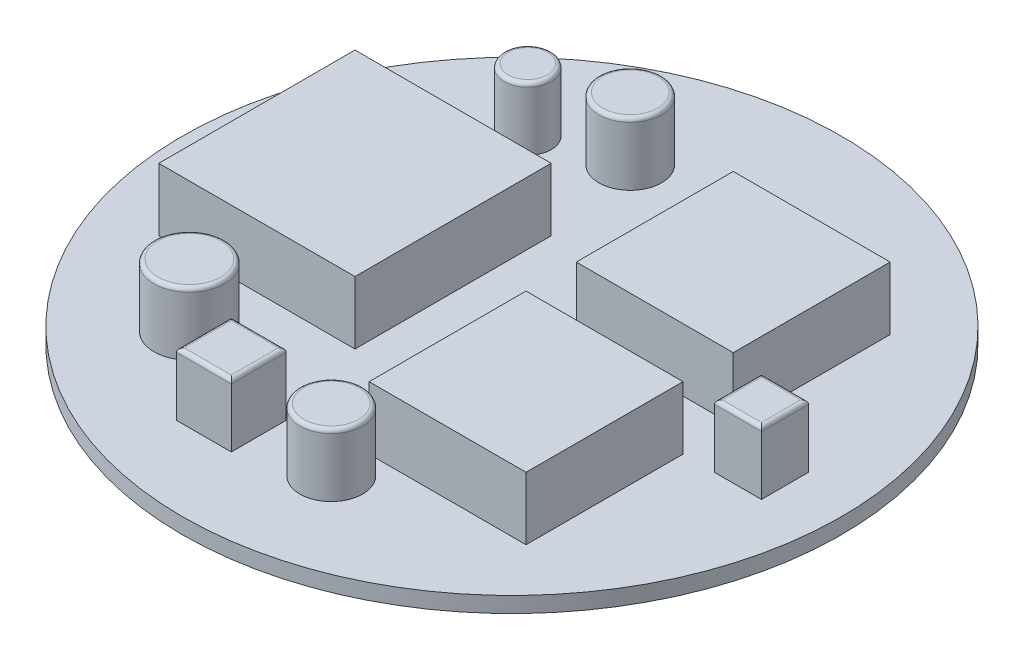
SolidWorks part; units mm, degrees
ref_plane "Front Plane" through (0, 0, 0) normal (0, 0, 1) x (1, 0, 0)
ref_plane "Top Plane" through (0, 0, 0) normal (0, 1, 0) x (1, 0, 0)
ref_plane "Right Plane" through (0, 0, 0) normal (1, 0, 0) x (0, 0, -1)
sketch "Sketch1" plane through (0, 0, 0) normal (0, 1, 0) x (1, 0, 0)
  circle A0 centre (0, 0) radius 42
extrude "Boss-Extrude1" add sketch "Sketch1" along normal blind 2
sketch "Sketch2" plane through (0, 2, 0) normal (0, 1, 0) x (1, 0, 0)
  line L0 (0, 0) -> (8.0339, 0) construction
  line L1 (-32.5, -12.5) -> (-7.5, -12.5)
  line L2 (-32.5, -12.5) -> (-32.5, 12.5)
  line L3 (-32.5, 12.5) -> (-7.5, 12.5)
  line L4 (-7.5, -12.5) -> (-7.5, 12.5)
  line L5 (-32.5, -12.5) -> (-7.5, 12.5) construction
  line L6 (-32.5, 12.5) -> (-7.5, -12.5) construction
  line L7 (5, 23.2036) -> (25, 23.2036)
  line L8 (5, 23.2036) -> (5, 3.2036)
  line L9 (5, 3.2036) -> (25, 3.2036)
  line L10 (25, 23.2036) -> (25, 3.2036)
  line L11 (5, 23.2036) -> (25, 3.2036) construction
  line L12 (5, 3.2036) -> (25, 23.2036) construction
  line L13 (25, -23.2036) -> (25, -3.2036)
  line L14 (5, -3.2036) -> (25, -3.2036)
  line L15 (5, -23.2036) -> (5, -3.2036)
  line L16 (5, -23.2036) -> (25, -23.2036)
  line L18 (-4.0182, -24.7434) -> (-11.0182, -24.7434)
  line L19 (-4.0182, -24.7434) -> (-4.0182, -31.7434)
  line L20 (-4.0182, -31.7434) -> (-11.0182, -31.7434)
  line L21 (-11.0182, -24.7434) -> (-11.0182, -31.7434)
  line L22 (-4.0182, -24.7434) -> (-11.0182, -31.7434) construction
  line L23 (-4.0182, -31.7434) -> (-11.0182, -24.7434) construction
  line L24 (29.0021, 2.7964) -> (35.0021, 2.7964)
  line L25 (29.0021, 2.7964) -> (29.0021, -3.2036)
  line L26 (29.0021, -3.2036) -> (35.0021, -3.2036)
  line L27 (35.0021, 2.7964) -> (35.0021, -3.2036)
  line L28 (29.0021, 2.7964) -> (35.0021, -3.2036) construction
  line L29 (29.0021, -3.2036) -> (35.0021, 2.7964) construction
  circle A2 centre (-20, 22.0202) radius 3
  circle A3 centre (-10.3025, 25.3777) radius 4
  circle A4 centre (-20, -21.1145) radius 4.5
  circle A5 centre (5, -28.0205) radius 4
  point P0 (-20, 0)
  point P7 (15, 13.2036)
  point P25 (-7.5182, -28.2434)
  point P30 (32.0021, -0.2036)
  dimension "D7" = 8
  dimension "D8" = 6
  dimension "D9" = 9
  dimension "D10" = 8
  dimension "D1" = 25
  dimension "D2" = 25
  dimension "D3" = 20
  dimension "D4" = 20
  dimension "D5" = 20
  dimension "D6" = 15
  dimension "D11" = 7
  dimension "D12" = 7
  dimension "D13" = 6
  dimension "D14" = 6
extrude "Boss-Extrude2" add sketch "Sketch2" along normal blind 8
sketch "Sketch3" plane through (0, 10, 0) normal (0, 1, 0) x (1, 0, 0)
  text T0 "GPS"
sketch "Sketch4" plane through (0, 10, 0) normal (0, 1, 0) x (1, 0, 0)
  text T0 "Heat"
sketch "Sketch5" plane through (0, 10, 0) normal (0, 1, 0) x (1, 0, 0)
  text T0 "Storage"
fillet "Fillet1" radius 0.5 12 edges at (32.0021, 10, -2.7964) (29.0021, 10, 0.2036) (32.0021, 10, 3.2036) (35.0021, 10, 0.2036) (5, 10, 32.0205) (-11.0182, 10, 28.2434) (-7.5182, 10, 24.7434) (-4.0182, 10, 28.2434) (-7.5182, 10, 31.7434) (-20, 10, 25.6145) (-10.3025, 10, -21.3777) (-20, 10, -19.0202)
sketch "Sketch6" plane through (0, 0, 0) normal (1, 0, 0) x (0, 0, -1)
  line L0 (0, 0) -> (0, -15.4086)
  line L1 (0, 0) -> (-25, 0)
  line L2 (-42, 0) -> (42, 0) construction
  line L3 (0, -15.4086) -> (-15.7638, -15.4086) construction
  arc A0 (-25, 0) -> (0, -15.4086) centre (0, 12.5766) ccw
  point P4 (0, 0)
  point P9 (0, -17.311)
  point P10 (0, 22.6924)
  point P11 (0, 12.5766)
  dimension "D1" = 25
revolve "Revolve1" add sketch "Sketch6" angle 360 about L0
